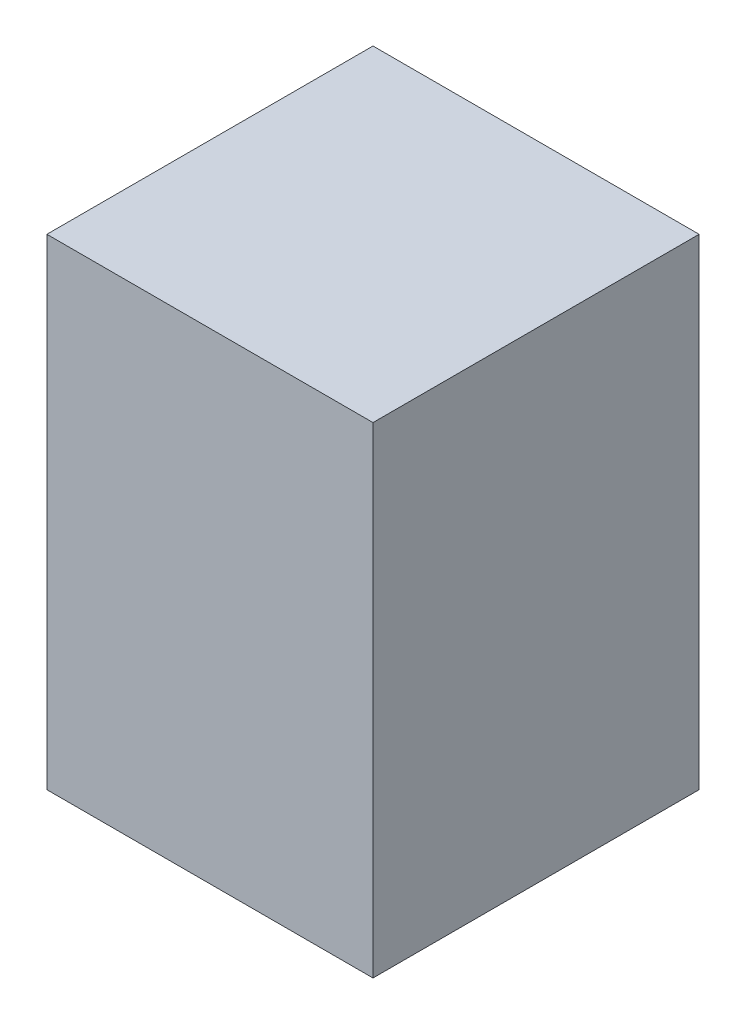
SolidWorks part; units mm, degrees
ref_plane "Front Plane" through (0, 0, 0) normal (0, 0, 1) x (1, 0, 0)
ref_plane "Top Plane" through (0, 0, 0) normal (0, 1, 0) x (1, 0, 0)
ref_plane "Right Plane" through (0, 0, 0) normal (1, 0, 0) x (0, 0, -1)
sketch "Sketch1" plane through (0, 0, 0) normal (0, 1, 0) x (1, 0, 0)
  line L1 (0, 0) -> (50.8, 0)
  line L2 (0, 0) -> (0, 50.8)
  line L3 (0, 50.8) -> (50.8, 50.8)
  line L4 (50.8, 0) -> (50.8, 50.8)
  dimension "D1" = 50.8
  dimension "D2" = 50.8
extrude "Boss-Extrude1" add sketch "Sketch1" along normal blind 74.93 contours L3 L4 L1 L2
